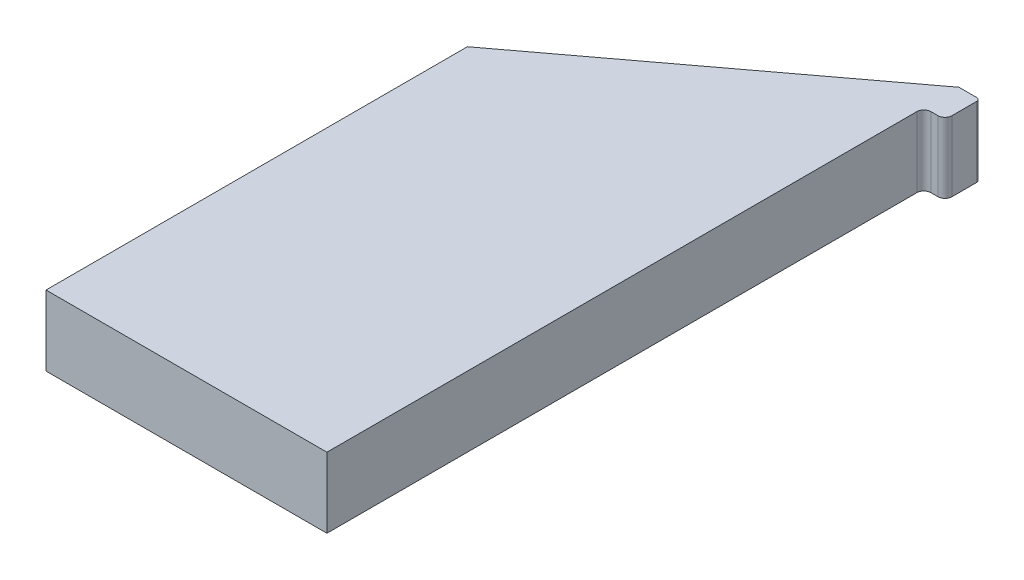
SolidWorks part; units mm, degrees
ref_plane "Front Plane" through (0, 0, 0) normal (0, 0, 1) x (1, 0, 0)
ref_plane "Top Plane" through (0, 0, 0) normal (0, 1, 0) x (1, 0, 0)
ref_plane "Right Plane" through (0, 0, 0) normal (1, 0, 0) x (0, 0, -1)
sketch "Sketch4" plane through (0, 0, 0) normal (0, 1, 0) x (1, 0, 0)
  line L0 (-10, 15) -> (10, 30)
  line L1 (-10, -15) -> (10, -15)
  line L2 (-10, -15) -> (-10, 15)
  line L4 (10, -15) -> (10, 15)
  line L5 (-10, -15) -> (10, 15) construction
  line L6 (-10, 15) -> (10, -15) construction
  line L7 (10, 30) -> (10, 15)
  point P0 (0, 0)
  dimension "D1" = 30
  dimension "D2" = 20
  dimension "D3" = 15
extrude "Boss-Extrude4" add sketch "Sketch4" along normal blind 5
sketch "Sketch6" plane through (0, 5, 0) normal (0, 1, 0) x (1, 0, 0)
  line L0 (10, 30) -> (11.25, 30)
  line L1 (11.5, 29.75) -> (11.5, 28)
  line L2 (11, 27.5) -> (10.5, 27.5)
  line L3 (10, -15) -> (10, 30) construction
  line L4 (10, 27) -> (10, 30)
  arc A0 (10.5, 27.5) -> (10, 27) centre (10.5, 27) ccw
  arc A1 (11.5, 28) -> (11, 27.5) centre (11, 28) cw
  arc A2 (11.5, 29.75) -> (11.25, 30) centre (11.25, 29.75) ccw
  point P8 (10, 28.4189)
  point P11 (11.7274, 28.8877)
  point P15 (11.5, 30)
  dimension "D1" = 0.5
  dimension "D2" = 0.5
  dimension "D4" = 0.25
  dimension "D3" = 1.5
  dimension "D5" = 3
extrude "Boss-Extrude5" add sketch "Sketch6" against normal up to surface (5 mm away) up to face at (0, 0, -3.75)
